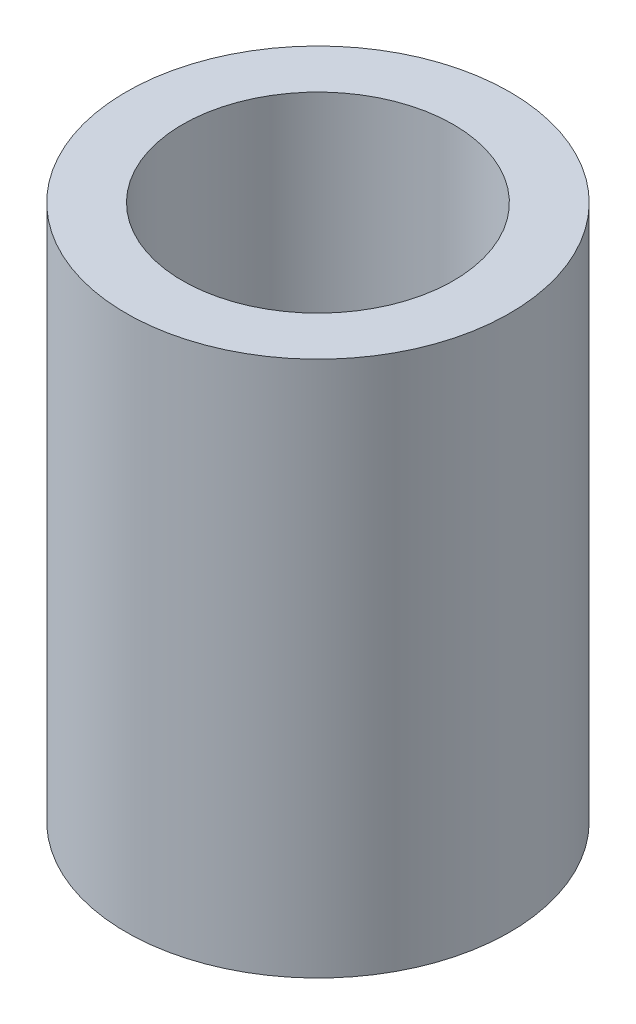
SolidWorks part; units mm, degrees
ref_plane "Front Plane" through (0, 0, 0) normal (0, 0, 1) x (1, 0, 0)
ref_plane "Top Plane" through (0, 0, 0) normal (0, 1, 0) x (1, 0, 0)
ref_plane "Right Plane" through (0, 0, 0) normal (1, 0, 0) x (0, 0, -1)
sketch "Croquis1" plane through (0, 0, 0) normal (0, 0, 1) x (1, 0, 0)
  line L0 (0, 0) -> (0, 51.4983) construction
  line L2 (24, 0) -> (34, 0)
  line L3 (24, 0) -> (24, 95)
  line L4 (24, 95) -> (34, 95)
  line L5 (34, 0) -> (34, 95)
  dimension "D1" = 48
  dimension "D2" = 10
  dimension "D3" = 95
revolve "Revolución1" add sketch "Croquis1" angle 360 about L0
equation "\"ID\" = 48"
equation "\"D1@Croquis1\"=\"ID\""
equation "\"Pared\"= 10"
equation "\"D2@Croquis1\"=\"Pared\""
equation "\"AlturaOlla\" = 95"
equation "\"D3@Croquis1\"=\"AlturaOlla\""
